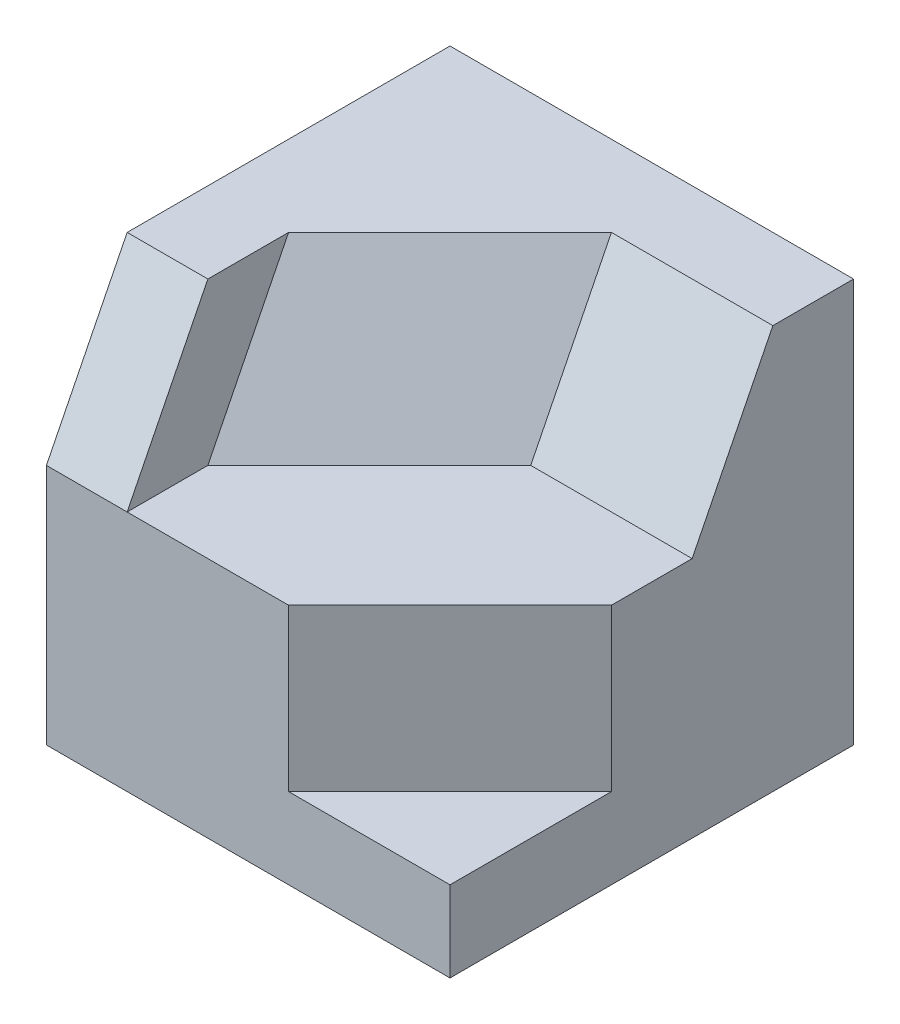
SolidWorks part; units mm, degrees
ref_plane "Front Plane" through (0, 0, 0) normal (0, 0, 1) x (1, 0, 0)
ref_plane "Top Plane" through (0, 0, 0) normal (0, 1, 0) x (1, 0, 0)
ref_plane "Right Plane" through (0, 0, 0) normal (1, 0, 0) x (0, 0, -1)
sketch "Sketch1" plane through (0, 0, 0) normal (0, 0, 1) x (1, 0, 0)
  line L1 (2.5, -2.5) -> (-2.5, -2.5)
  line L2 (2.5, -2.5) -> (2.5, 2.5)
  line L3 (2.5, 2.5) -> (-2.5, 2.5)
  line L4 (-2.5, -2.5) -> (-2.5, 2.5)
  line L5 (2.5, -2.5) -> (-2.5, 2.5) construction
  line L6 (2.5, 2.5) -> (-2.5, -2.5) construction
  point P0 (0, 0)
  dimension "D1" = 5
  dimension "D2" = 5
extrude "Boss-Extrude1" add sketch "Sketch1" along normal blind 5
sketch "Sketch2" plane through (0, 2.5, 0) normal (0, 1, 0) x (1, 0, 0)
  line L0 (2.5, -5) -> (2.5, -3)
  line L1 (2.5, -5) -> (2.5, 0) construction
  line L2 (2.5, -3) -> (0.5, -5)
  line L3 (2.5, -5) -> (-2.5, -5) construction
  line L4 (0.5, -5) -> (2.5, -5)
  dimension "D1" = 2
  dimension "D2" = 2
extrude "Cut-Extrude1" cut sketch "Sketch2" against normal blind 4
sketch "Sketch4" plane through (-2.5, 0, 0) normal (-1, 0, 0) x (0, 0, 1)
  line L0 (5, 2.5) -> (4, 2.5)
  line L1 (5, 2.5) -> (0, 2.5) construction
  line L2 (4, 2.5) -> (5, 0.5)
  line L3 (5, 2.5) -> (5, -2.5) construction
  line L4 (5, 0.5) -> (5, 2.5)
  dimension "D1" = 1
  dimension "D2" = 2
extrude "Cut-Extrude2" cut sketch "Sketch4" against normal blind 1
sketch "Sketch5" plane through (0, 0, 5) normal (0, 0, 1) x (1, 0, 0)
  line L0 (2.5, 2.5) -> (0.5, 2.5)
  line L1 (0.5, 2.5) -> (0.5, 0.5)
  line L2 (0.5, -1.5) -> (0.5, 2.5) construction
  line L3 (0.5, 0.5) -> (2.5, 0.5)
  line L4 (2.5, -1.5) -> (2.5, 2.5) construction
  line L5 (2.5, 0.5) -> (2.5, 2.5)
  dimension "D1" = 2
extrude "Cut-Extrude9" cut sketch "Sketch5" against normal blind 3
sketch "Sketch10" plane through (2.5, 0, 0) normal (1, 0, 0) x (0, 0, -1)
  line L0 (-1, 2.5) -> (-2, 0.5)
  line L1 (-2, 2.5) -> (0, 2.5) construction
  line L2 (-2, 0.5) -> (-2, 2.5)
  line L3 (-2, 2.5) -> (-1, 2.5)
  dimension "D1" = 1
extrude "Cut-Extrude10" cut sketch "Sketch10" against normal blind 2
sketch "Sketch11" plane through (0.5, 0, 0) normal (1, 0, 0) x (0, 0, -1)
  line L0 (-5, 2.5) -> (-4, 2.5)
  line L1 (-1, 2.5) -> (-5, 2.5) construction
  line L2 (-4, 2.5) -> (-4, 0.5)
  line L3 (-3, 0.5) -> (-5, 0.5) construction
  line L4 (-4, 0.5) -> (-5, 0.5)
  line L5 (-5, 0.5) -> (-5, 2.5)
  dimension "D1" = 1
extrude "Cut-Extrude11" cut sketch "Sketch11" against normal blind 2
sketch "Sketch15" plane through (0, 2.5, 0) normal (0, 1, 0) x (1, 0, 0)
  line L0 (0.5, -1) -> (-1.5, -3)
  dimension "D1" = 1
ref_plane "Plane6" through (1.2222, 0.6111, 1.2222) normal (-0.6667, -0.3333, -0.6667) x (-0.7454, 0.2981, 0.5963)
sketch "Sketch16" plane through (1.2222, 0.6111, 1.2222) normal (-0.6667, -0.3333, -0.6667) x (-0.7454, 0.2981, 0.5963)
  line L0 (0.969, -0.4472) -> (0.969, 1.7889)
  line L1 (0.969, 1.7889) -> (3.6522, 0.8944)
  line L2 (0.969, 1.7889) -> (3.6522, 0.8944) construction
  line L3 (3.6522, 0.8944) -> (3.6522, -1.3416)
  line L4 (3.6522, -1.3416) -> (0.969, -0.4472)
extrude "Cut-Extrude14" cut sketch "Sketch16" against normal through all
sketch "Sketch17" plane through (-1.5, 0, 0) normal (1, 0, 0) x (0, 0, -1)
  line L0 (-3, 2.5) -> (-4, 0.5)
  line L1 (-4, 0.5) -> (-4, 2.5)
  line L2 (-4, 2.5) -> (-3, 2.5)
extrude "Cut-Extrude15" cut sketch "Sketch17" along normal blind 2
sketch "Sketch18" plane through (0, 0.5, 0) normal (0, 1, 0) x (1, 0, 0)
  line L0 (0.5, -4) -> (0.5, -2)
  line L1 (0.5, -2) -> (-1.5, -4)
  line L2 (-1.5, -4) -> (0.5, -4)
extrude "Cut-Extrude16" cut sketch "Sketch18" along normal blind 2
